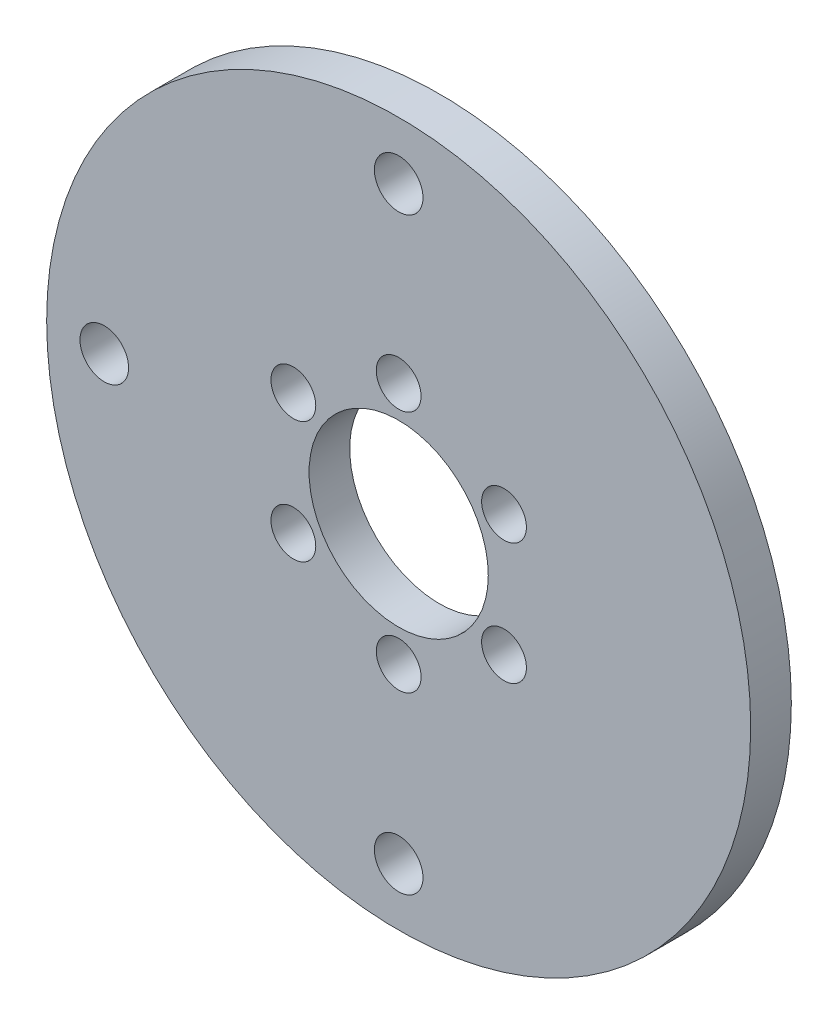
SolidWorks part; units mm, degrees
material "Balsa"
ref_plane "Front Plane" through (0, 0, 0) normal (0, 0, 1) x (1, 0, 0)
ref_plane "Top Plane" through (0, 0, 0) normal (0, 1, 0) x (1, 0, 0)
ref_plane "Right Plane" through (0, 0, 0) normal (1, 0, 0) x (0, 0, -1)
sketch "Sketch1" plane through (0, 0, 0) normal (0, 0, 1) x (1, 0, 0)
  circle A0 centre (0, 0) radius 27.5
  circle A1 centre (0, 0) radius 7
  circle A2 centre (0, 0) radius 23 construction
  circle A3 centre (0, 23) radius 1.8986
  circle A4 centre (16.2635, 16.2635) radius 1.5 construction
  circle A5 centre (23, 0) radius 1.8986 construction
  circle A6 centre (16.2635, -16.2635) radius 1.5 construction
  circle A7 centre (0, -23) radius 1.8986
  circle A8 centre (-16.2635, -16.2635) radius 1.5 construction
  circle A9 centre (-23, 0) radius 1.8986
  circle A10 centre (-16.2635, 16.2635) radius 1.5 construction
  circle A11 centre (0, 0) radius 9.5 construction
  circle A12 centre (0, 9.5) radius 1.75
  circle A13 centre (8.2272, 4.75) radius 1.75
  circle A14 centre (8.2272, -4.75) radius 1.75
  circle A15 centre (0, -9.5) radius 1.75
  circle A16 centre (-8.2272, -4.75) radius 1.75
  circle A17 centre (-8.2272, 4.75) radius 1.75
  dimension "D1" = 55
  dimension "D2" = 14
  dimension "D4" = 46
  dimension "D5" = 3.7973
  dimension "D6" = 3
  dimension "D8" = 3.5
  dimension "D10" = 19
  dimension "D3" = 45
  dimension "D9" = 60
  dimension "D7" = 4
  dimension "D11" = 3
extrude "Boss-Extrude1" add sketch "Sketch1" along normal blind 3.175
other "Move Face1" [suppressed] parameters "D1"=0.08
